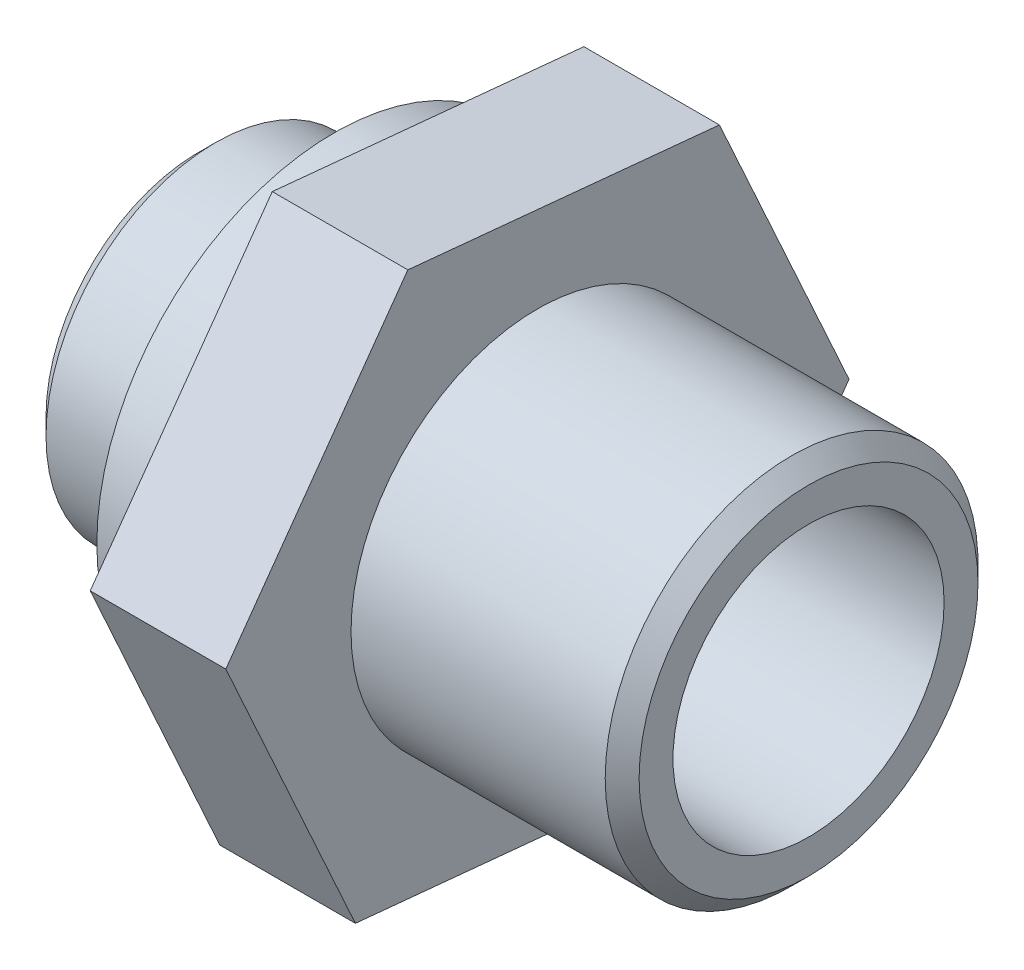
SolidWorks part; units mm, degrees
material "Stainless Steel (ferritic)"
ref_plane "Front Plane" through (0, 0, 0) normal (0, 0, 1) x (1, 0, 0)
ref_plane "Top Plane" through (0, 0, 0) normal (0, 1, 0) x (1, 0, 0)
ref_plane "Right Plane" through (0, 0, 0) normal (1, 0, 0) x (0, 0, -1)
sketch "Sketch1" plane through (0, 0, 0) normal (0, 0, 1) x (1, 0, 0)
  line L0 (-4.5, 0) -> (-1.5, 0)
  line L1 (-4.5, 0) -> (-4.5, -2.25)
  line L2 (-4.25, -2.5) -> (-2.5, -2.5)
  line L3 (-2.5, -2.5) -> (-2.5, -3.5)
  line L4 (-2.5, -3.5) -> (-1.5, -3.5)
  line L8 (0.5, -2.75) -> (4.25, -2.75)
  line L9 (4.5, 0) -> (4.5, -2.5)
  line L10 (-4.5, -2.25) -> (-4.25, -2.5)
  line L11 (4.25, -2.75) -> (4.5, -2.5)
  line L12 (0.5, -2.75) -> (0.5, 0)
  line L13 (-1.5, -3.5) -> (-1.5, 0)
  line L14 (0.5, 0) -> (4.5, 0)
  point P4 (0, 0)
  point P6 (-4.5, -2.5)
  point P14 (4.5, -2.75)
  dimension "D1" = 9
  dimension "D2" = 2.75
  dimension "D3" = 2.5
  dimension "D4" = 1
  dimension "D5" = 2
  dimension "D6" = 0.25
  dimension "D7" = 45
  dimension "D8" = 0.25
  dimension "D9" = 45
  dimension "D10" = 1
revolve "Revolve1" add sketch "Sketch1" angle 360 about L0
sketch "Sketch5" plane through (-1.5, 0, 0) normal (1, 0, 0) x (0, 0, -1)
  line L1 (1.9117, -4.2046) -> (4.5971, -0.4467)
  line L2 (4.5971, -0.4467) -> (2.6854, 3.7579)
  line L3 (2.6854, 3.7579) -> (-1.9117, 4.2046)
  line L4 (-1.9117, 4.2046) -> (-4.5971, 0.4467)
  line L5 (-4.5971, 0.4467) -> (-2.6854, -3.7579)
  line L6 (-2.6854, -3.7579) -> (1.9117, -4.2046)
  circle A0 centre (0, 0) radius 4 construction
  dimension "D1" = 8
extrude "Boss-Extrude2" add sketch "Sketch5" along normal blind 2
sketch "Sketch9" plane through (4.5, 0, 0) normal (1, 0, 0) x (0, 0, -1)
  circle A0 centre (0, 0) radius 2
  dimension "4" = 4
extrude "Cut-Extrude1" cut sketch "Sketch9" against normal blind 10
